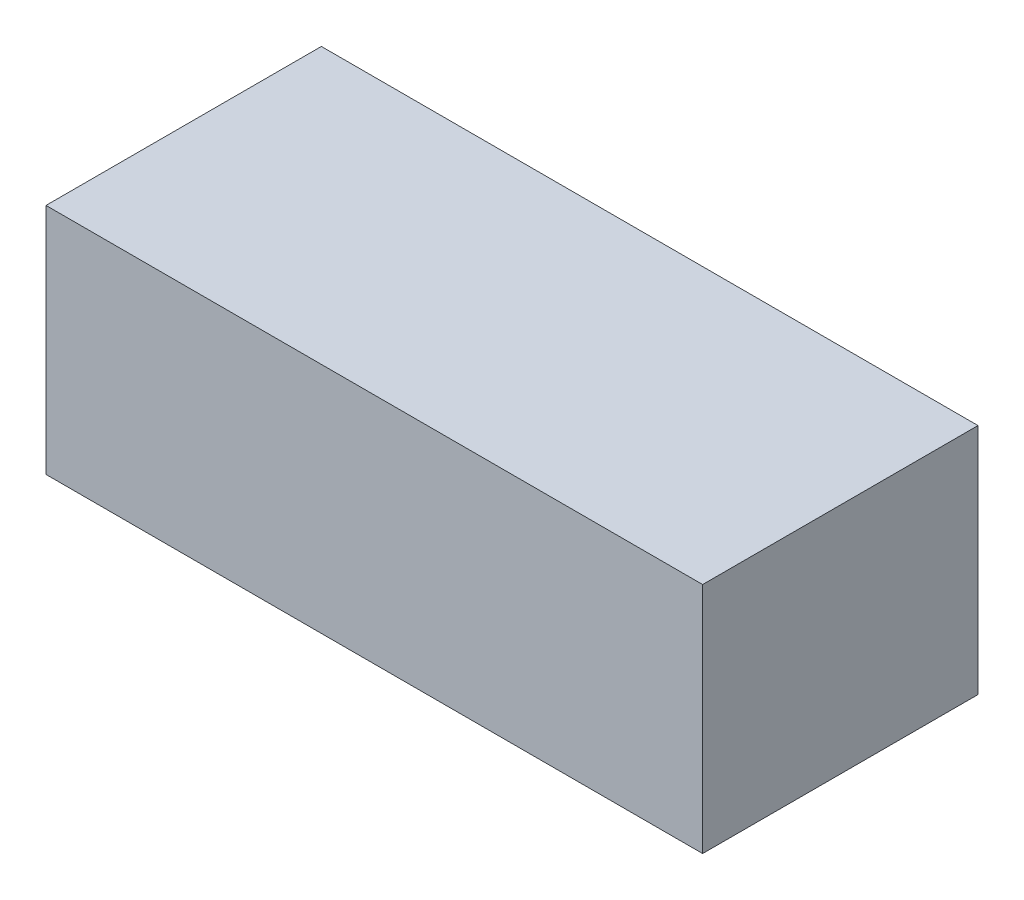
SolidWorks part; units mm, degrees
ref_plane "Front Plane" through (0, 0, 0) normal (0, 0, 1) x (1, 0, 0)
ref_plane "Top Plane" through (0, 0, 0) normal (0, 1, 0) x (1, 0, 0)
ref_plane "Right Plane" through (0, 0, 0) normal (1, 0, 0) x (0, 0, -1)
sketch "Sketch1" plane through (0, 0, 0) normal (0, 1, 0) x (1, 0, 0)
  line L1 (-15.6314, 13.464) -> (15.3686, 13.464)
  line L2 (-15.6314, 13.464) -> (-15.6314, 0.464)
  line L3 (-15.6314, 0.464) -> (15.3686, 0.464)
  line L4 (15.3686, 13.464) -> (15.3686, 0.464)
  dimension "D1" = 31
  dimension "D2" = 13
extrude "Boss-Extrude1" add sketch "Sketch1" along normal blind 11
